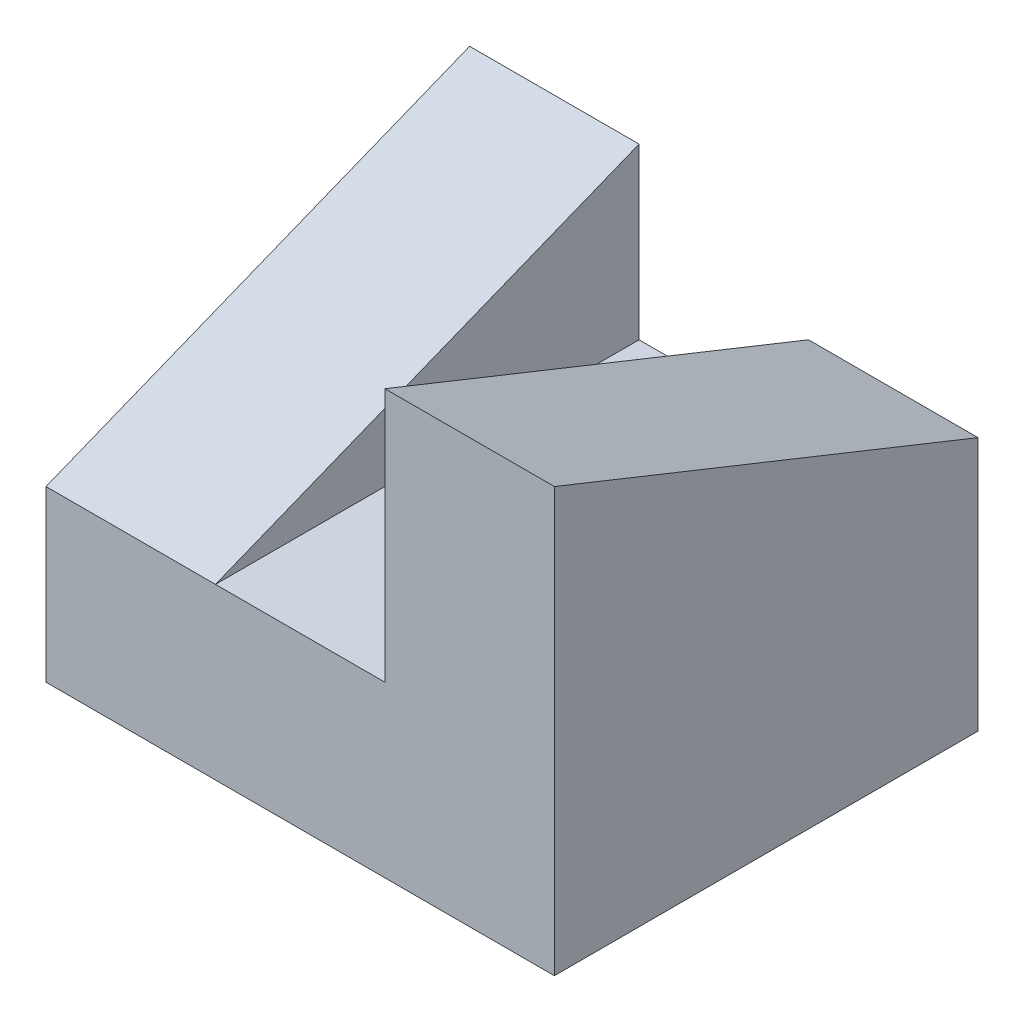
SolidWorks part; units mm, degrees
ref_plane "Front Plane" through (0, 0, 0) normal (0, 0, 1) x (1, 0, 0)
ref_plane "Top Plane" through (0, 0, 0) normal (0, 1, 0) x (1, 0, 0)
ref_plane "Right Plane" through (0, 0, 0) normal (1, 0, 0) x (0, 0, -1)
sketch "Sketch1" plane through (0, 0, 0) normal (0, 0, 1) x (1, 0, 0)
  line L0 (-30, 10) -> (-10, 10)
  line L1 (-10, 10) -> (-10, 15)
  line L2 (-10, 15) -> (0, 15)
  line L3 (0, 15) -> (0, 0)
  line L4 (0, 0) -> (-30, 0)
  line L5 (-30, 0) -> (-30, 10)
  dimension "D1" = 10
  dimension "D2" = 5
  dimension "D3" = 15
  dimension "D4" = 20
extrude "Boss-Extrude1" add sketch "Sketch1" along normal blind 25
sketch "Sketch2" plane through (-30, 0, 0) normal (-1, 0, 0) x (0, 0, 1)
  line L0 (0, 10) -> (0, 20)
  line L1 (0, 20) -> (25, 10)
  line L2 (25, 10) -> (0, 10)
  dimension "D1" = 10
extrude "Boss-Extrude2" add sketch "Sketch2" against normal blind 10
sketch "Sketch3" plane through (0, 0, 0) normal (1, 0, 0) x (0, 0, -1)
  line L0 (-25, 15) -> (-25, 25)
  line L1 (-25, 25) -> (0, 15)
  line L2 (0, 15) -> (-25, 15)
  dimension "D1" = 10
extrude "Boss-Extrude3" add sketch "Sketch3" against normal blind 10
